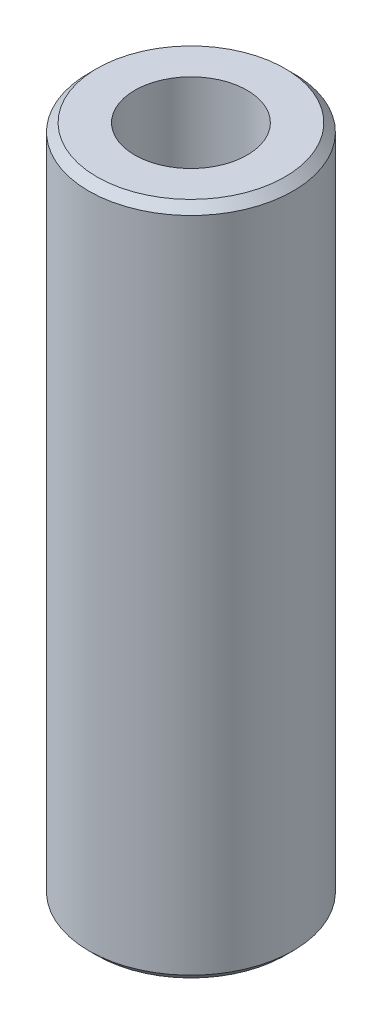
SolidWorks part; units mm, degrees
material "ABS"
ref_plane "Front Plane" through (0, 0, 0) normal (0, 0, 1) x (1, 0, 0)
ref_plane "Top Plane" through (0, 0, 0) normal (0, 1, 0) x (1, 0, 0)
ref_plane "Right Plane" through (0, 0, 0) normal (1, 0, 0) x (0, 0, -1)
sketch "Sketch1" plane through (0, 0, 0) normal (0, 1, 0) x (1, 0, 0)
  circle A0 centre (0, 0) radius 2.75
  circle A1 centre (0, 0) radius 5
  dimension "D1" = 5.5
  dimension "D2" = 10
extrude "Boss-Extrude1" add sketch "Sketch1" along normal mid plane 33
chamfer "Chamfer1" distance 0.4 angle 45 2 edges at (0, -16.5, 5) (0, 16.5, 5)
